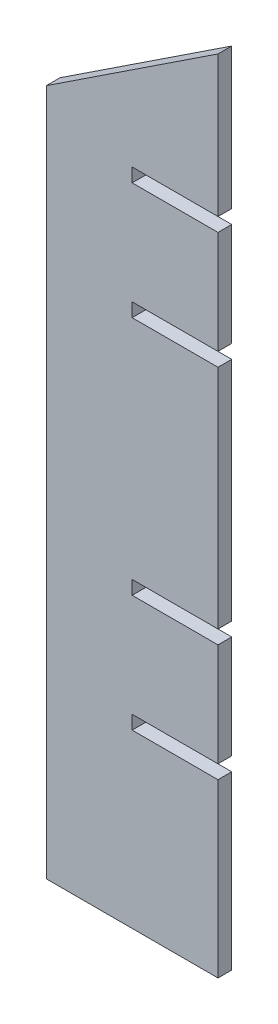
SolidWorks part; units mm, degrees
ref_plane "Plan de face" through (0, 0, 0) normal (0, 0, 1) x (1, 0, 0)
ref_plane "Plan de dessus" through (0, 0, 0) normal (0, 1, 0) x (1, 0, 0)
ref_plane "Plan de droite" through (0, 0, 0) normal (1, 0, 0) x (0, 0, -1)
sketch "Esquisse1" plane through (0, 0, 0) normal (0, 0, 1) x (1, 0, 0)
  line L0 (-114.0649, 137.6822) -> (-114.0649, -62.3178)
  line L1 (-114.0649, -62.3178) -> (-64.0649, -62.3178)
  line L2 (-64.0649, -62.3178) -> (-64.0649, -12.3178)
  line L3 (-64.0649, -12.3178) -> (-89.0649, -12.3178)
  line L4 (-89.0649, -12.3178) -> (-89.0649, -8.3178)
  line L5 (-89.0649, -8.3178) -> (-64.0649, -8.3178)
  line L6 (-64.0649, -8.3178) -> (-64.0649, 21.6822)
  line L7 (-64.0649, 91.6822) -> (-89.0649, 91.6822)
  line L8 (-89.0649, 91.6822) -> (-89.0649, 95.6822)
  line L9 (-89.0649, 95.6822) -> (-64.0649, 95.6822)
  line L10 (-64.0649, 21.6822) -> (-89.0649, 21.6822)
  line L11 (-64.0649, 170.6822) -> (-114.0649, 137.6822)
  line L12 (-64.0649, 170.6822) -> (-114.0649, 170.6822) construction
  line L13 (-89.0649, 21.6822) -> (-89.0649, 25.6822)
  line L14 (-89.0649, 25.6822) -> (-64.0649, 25.6822)
  line L15 (-64.0649, 25.6822) -> (-64.0649, 91.6822)
  line L16 (-64.0649, 95.6822) -> (-64.0649, 125.6822)
  line L17 (-64.0649, 125.6822) -> (-89.0649, 125.6822)
  line L18 (-89.0649, 125.6822) -> (-89.0649, 129.6822)
  line L19 (-89.0649, 129.6822) -> (-64.0649, 129.6822)
  line L20 (-64.0649, 129.6822) -> (-64.0649, 170.6822)
  dimension "D1" = 4
  dimension "D2" = 25
  dimension "D3" = 200
  dimension "D4" = 50
  dimension "D5" = 50
  dimension "D6" = 30
  dimension "D7" = 30
  dimension "D8" = 66
  dimension "D9" = 41
extrude "Boss.-Extru.1" add sketch "Esquisse1" along normal blind 4
